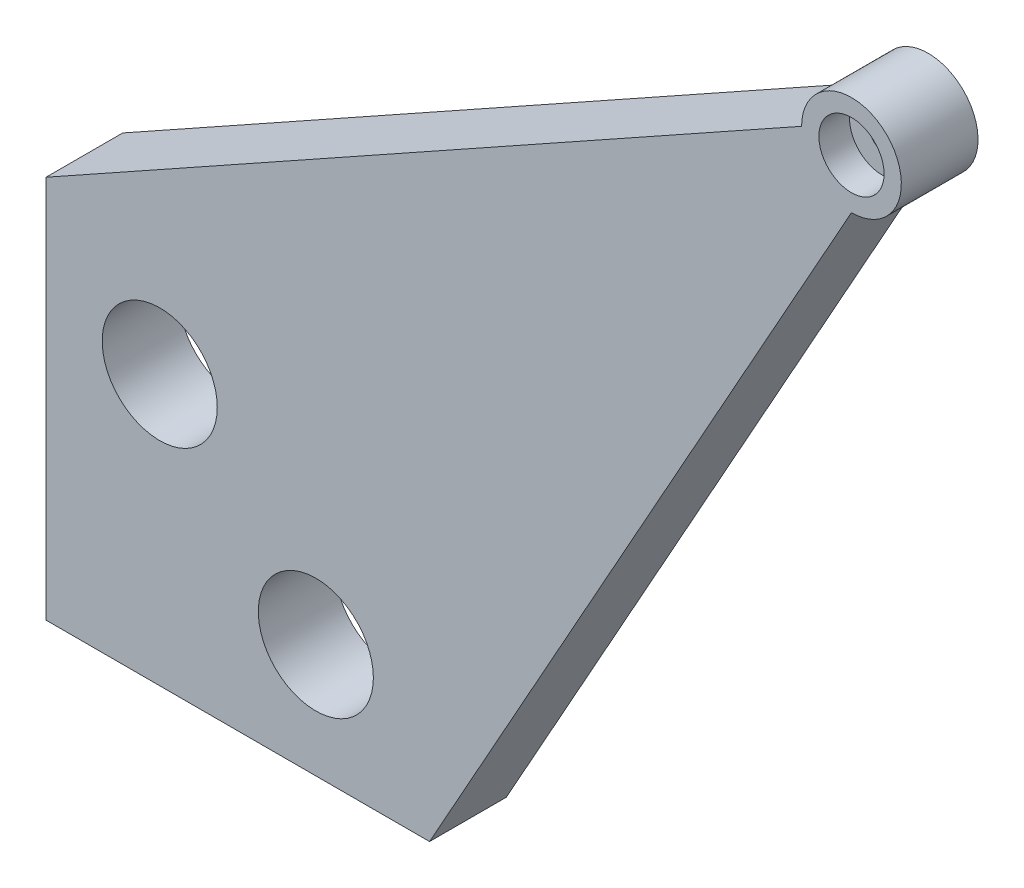
SolidWorks part; units mm, degrees
ref_plane "Plano frontal" through (0, 0, 0) normal (0, 0, 1) x (1, 0, 0)
ref_plane "Plano superior" through (0, 0, 0) normal (0, 1, 0) x (1, 0, 0)
ref_plane "Plano direito" through (0, 0, 0) normal (1, 0, 0) x (0, 0, -1)
sketch "Esboço3" plane through (0, 0, 0) normal (0, 0, 1) x (1, 0, 0)
  line L0 (-62.966, 0) -> (106.6858, 0) construction
  line L1 (0, 69.7378) -> (0, -73.302) construction
  line L2 (0, 50) -> (98.5, 105)
  line L3 (0, 0) -> (50, 0)
  line L4 (0, 0) -> (0, 50)
  line L7 (50, 0) -> (105, 98.5)
  arc A0 (105, 98.5) -> (98.5, 105) centre (105, 105) ccw
  dimension "D4" = 105
  dimension "D5" = 13
  dimension "D3" = 105
extrude "Ressalto-extrusão2" add sketch "Esboço3" along normal mid plane 10
sketch "Esboço4" plane through (0, 0, 5) normal (0, 0, 1) x (1, 0, 0)
  circle A0 centre (105, 105) radius 4.25
  arc A1 (105, 98.5) -> (98.5, 105) centre (105, 105) ccw construction
  dimension "D1" = 8.5
extrude "Corte-extrusão1" cut sketch "Esboço4" against normal blind 4 contours A0
sketch "Esboço5" plane through (0, 0, 1) normal (0, 0, 1) x (1, 0, 0)
  circle A0 centre (105, 105) radius 1.5
  circle A1 centre (105, 105) radius 4.25 construction
extrude "Corte-extrusão2" cut sketch "Esboço5" against normal through all
sketch "Esboço6" plane through (0, 0, 5) normal (0, 0, 1) x (1, 0, 0)
  line L0 (-26.6702, 0) -> (72.5742, 0) construction
  line L1 (0, 62.2144) -> (0, -11.4301) construction
  line L2 (0, 50) -> (63.2897, 50) construction
  line L3 (50, 0) -> (50, 50) construction
  line L4 (0, 50) -> (14.8256, 35.1744) construction
  line L5 (14.8256, 35.1744) -> (35.1744, 14.8256) construction
  line L6 (35.1744, 14.8256) -> (50, 0) construction
  line L7 (0, 0) -> (50, 50) construction
  circle A0 centre (14.8256, 35.1744) radius 7.5
  circle A1 centre (35.1744, 14.8256) radius 7.5
  dimension "D1" = 15
  dimension "D2" = 15
extrude "Corte-extrusão3" cut sketch "Esboço6" against normal through all
